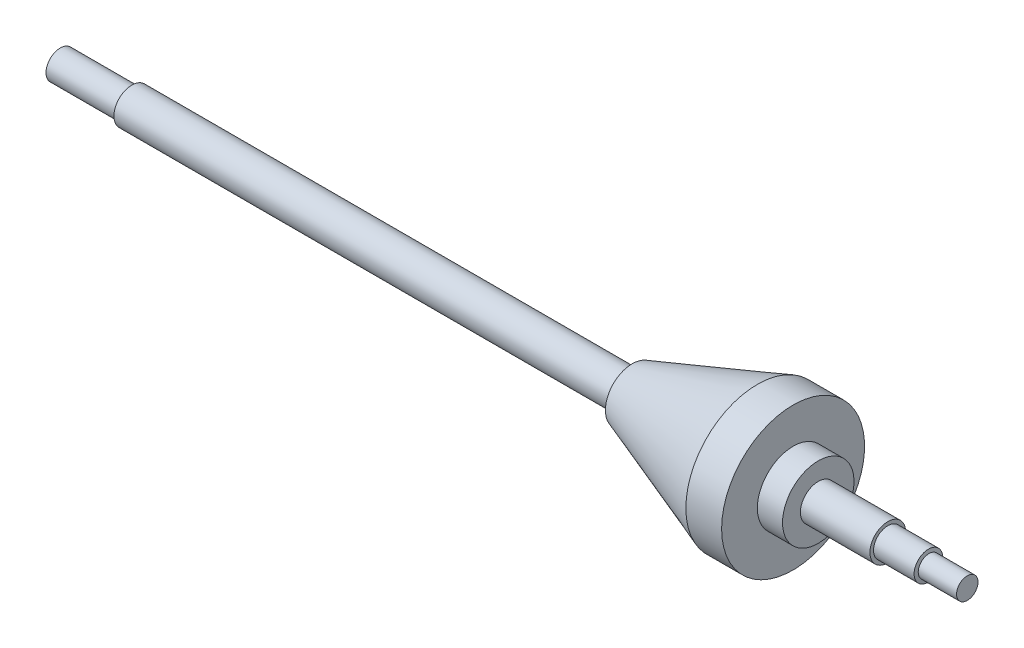
SolidWorks part; units mm, degrees
ref_plane "Front Plane" through (0, 0, 0) normal (0, 0, 1) x (1, 0, 0)
ref_plane "Top Plane" through (0, 0, 0) normal (0, 1, 0) x (1, 0, 0)
ref_plane "Right Plane" through (0, 0, 0) normal (1, 0, 0) x (0, 0, -1)
sketch "Sketch1" plane through (0, 0, 0) normal (0, 1, 0) x (1, 0, 0)
  line L0 (0, 0) -> (300.3357, 0) construction
  line L1 (0, 0) -> (0, -4)
  line L2 (0, -4) -> (20, -4)
  line L3 (20, -4) -> (20, -5)
  line L4 (20, -5) -> (160, -5)
  line L5 (160, -5) -> (160, -7.5)
  line L6 (195, -20) -> (160, -7.5)
  line L7 (195, -20) -> (205, -20)
  line L8 (205, -20) -> (205, -10)
  line L9 (205, -10) -> (212.041, -10)
  line L10 (212.041, -10) -> (212.041, -5)
  line L11 (212.041, -5) -> (231.4962, -5)
  line L12 (231.4962, -5) -> (231.4962, -4)
  line L13 (231.4962, -4) -> (242.8517, -4)
  line L14 (242.8517, -4) -> (243.0062, -3)
  line L15 (243.0062, -3) -> (253.734, -3)
  line L16 (253.734, -3) -> (253.734, 0)
  line L17 (0, 0) -> (253.734, 0)
  point P3 (212.041, -6.4101)
  point P20 (231.4962, -4.1164)
  point P21 (243.0062, -2.6828)
  point P22 (248.3701, -3)
  dimension "D1" = 185
  dimension "D2" = 20
  dimension "D3" = 45
  dimension "D4" = 10
  dimension "D5" = 15
  dimension "D6" = 8
  dimension "D7" = 10
  dimension "D8" = 40
  dimension "D9" = 20
  dimension "D10" = 10
  dimension "D11" = 8
  dimension "D12" = 6
revolve "Revolve1" add sketch "Sketch1" angle 360 about L0
